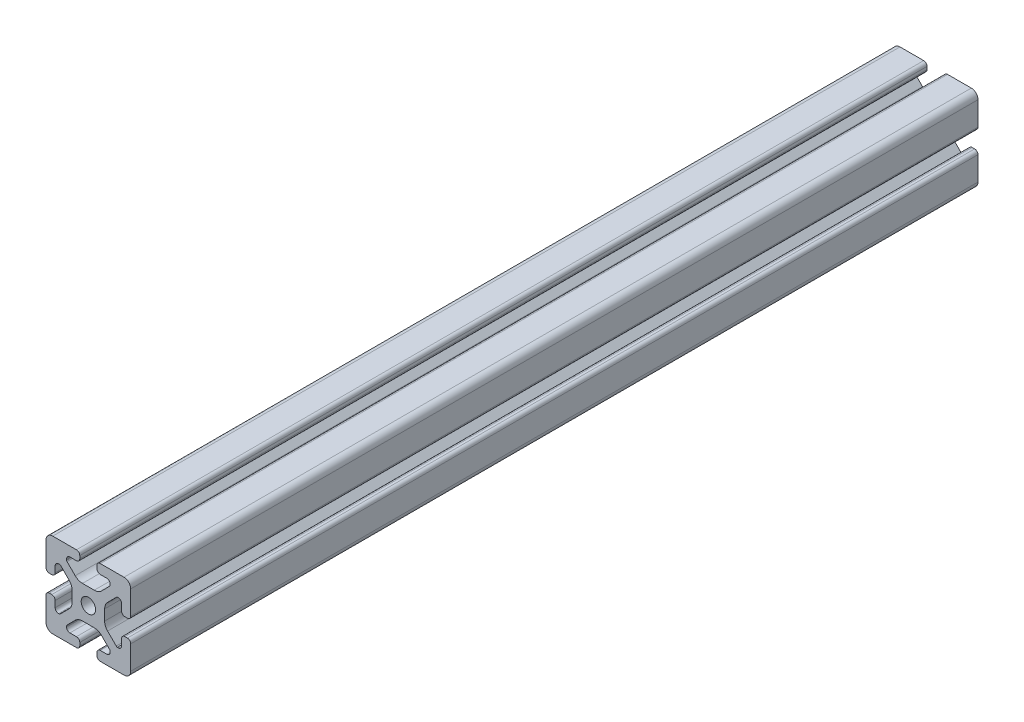
SolidWorks part; units mm, degrees
ref_plane "Front Plane" through (0, 0, 0) normal (0, 0, 1) x (1, 0, 0)
ref_plane "Top Plane" through (0, 0, 0) normal (0, 1, 0) x (1, 0, 0)
ref_plane "Right Plane" through (0, 0, 0) normal (1, 0, 0) x (0, 0, -1)
sketch "Sketch1" plane through (0, 0, 0) normal (0, 0, 1) x (1, 0, 0)
  line L0 (0, 19.7407) -> (0, -19.7407) construction
  line L1 (19.0335, 0) -> (-20.7246, 0) construction
  line L2 (-8.715, -15.5246) -> (-5.63, -15.5246)
  line L3 (-10.285, -13.9546) -> (-10.285, -13.4925)
  line L4 (-6.2171, -9.1098) -> (-10.0624, -12.9551)
  line L5 (2.7773, -7.685) -> (-2.7773, -7.685)
  line L6 (10.0624, -12.9551) -> (6.2171, -9.1098)
  line L7 (10.285, -13.9546) -> (10.285, -13.4925)
  line L8 (5.63, -15.5246) -> (8.715, -15.5246)
  line L9 (4.06, -18.43) -> (4.06, -17.0946)
  line L10 (-4.06, -18.43) -> (-4.06, -17.0946)
  line L11 (15.68, -8.7154) -> (15.68, -5.63)
  line L12 (-14.11, -10.2854) -> (-13.8169, -10.2854)
  line L13 (20, -16.83) -> (20, -5.63)
  line L14 (20, 5.63) -> (20, 13.0011)
  line L15 (-16.83, 20) -> (-5.63, 20)
  line L16 (5.63, 20) -> (12.9796, 20)
  line L17 (-8.715, 15.5246) -> (-5.63, 15.5246)
  line L18 (-20, -17.0184) -> (-20, -5.7579)
  line L19 (-20, 5.573) -> (-20, 13.0045)
  line L20 (-15.68, -8.7154) -> (-15.68, -5.7579)
  line L21 (-16.6746, -20) -> (-5.63, -20)
  line L22 (5.63, -20) -> (13, -20)
  line L23 (14.11, -10.2854) -> (13.6201, -10.2854)
  line L24 (13.1637, -9.947) -> (9.0762, -5.8595)
  line L25 (7.685, -2.5008) -> (7.685, 2.5008)
  line L26 (9.0762, 5.8595) -> (13.2795, 10.0628)
  line L27 (13.8169, 10.2854) -> (14.11, 10.2854)
  line L28 (15.68, 8.7154) -> (15.68, 5.63)
  line L29 (17.25, 4.06) -> (18.43, 4.06)
  line L30 (20, 13.0011) -> (20, 16.83)
  line L31 (16.83, 20) -> (12.9796, 20)
  line L32 (4.06, 18.43) -> (4.06, 17.0946)
  line L33 (5.63, 15.5246) -> (8.715, 15.5246)
  line L34 (10.285, 13.9546) -> (10.285, 13.4925)
  line L35 (10.0624, 12.9551) -> (6.2171, 9.1098)
  line L36 (2.7773, 7.685) -> (-2.7773, 7.685)
  line L37 (-6.2171, 9.1098) -> (-10.0624, 12.9551)
  line L38 (-10.285, 13.4925) -> (-10.285, 13.9546)
  line L39 (-4.06, 17.0946) -> (-4.06, 18.43)
  line L40 (-20, 16.83) -> (-20, 13.0045)
  line L41 (-18.43, 4.003) -> (-17.25, 4.003)
  line L42 (-15.68, 5.573) -> (-15.68, 8.4757)
  line L43 (-14.0552, 10.0447) -> (-13.7199, 10.033)
  line L44 (-13.0405, 9.8238) -> (-9.0762, 5.8595)
  line L45 (-7.685, 2.5008) -> (-7.685, -2.5008)
  line L46 (-9.0762, -5.8595) -> (-13.2795, -10.0628)
  line L47 (-17.2485, -4.1204) -> (-18.43, -4.1204)
  line L48 (13, -20) -> (16.83, -20)
  line L49 (18.43, -4.06) -> (17.25, -4.06)
  arc A0 (-5.63, -15.5246) -> (-4.06, -17.0946) centre (-5.63, -17.0946) cw
  arc A1 (-8.715, -15.5246) -> (-10.285, -13.9546) centre (-8.715, -13.9546) cw
  arc A2 (-10.285, -13.4925) -> (-10.0624, -12.9551) centre (-9.525, -13.4925) cw
  arc A3 (-6.2171, -9.1098) -> (-2.7773, -7.685) centre (-2.7773, -12.5496) cw
  arc A4 (2.7773, -7.685) -> (6.2171, -9.1098) centre (2.7773, -12.5496) cw
  arc A5 (10.0624, -12.9551) -> (10.285, -13.4925) centre (9.525, -13.4925) cw
  arc A6 (10.285, -13.9546) -> (8.715, -15.5246) centre (8.715, -13.9546) cw
  arc A7 (4.06, -17.0946) -> (5.63, -15.5246) centre (5.63, -17.0946) cw
  arc A8 (5.63, -20) -> (4.06, -18.43) centre (5.63, -18.43) cw
  arc A9 (-4.06, -18.43) -> (-5.63, -20) centre (-5.63, -18.43) cw
  circle A10 centre (0, 0) radius 3.4
  arc A11 (17.25, -4.06) -> (15.68, -5.63) centre (17.25, -5.63) ccw
  arc A12 (14.11, -10.2854) -> (15.68, -8.7154) centre (14.11, -8.7154) ccw
  arc A13 (13.1637, -9.947) -> (13.6201, -10.2854) centre (13.8117, -9.55) ccw
  arc A14 (7.685, -2.5008) -> (9.0762, -5.8595) centre (12.435, -2.5008) ccw
  arc A15 (9.0762, 5.8595) -> (7.685, 2.5008) centre (12.435, 2.5008) ccw
  arc A16 (13.8169, 10.2854) -> (13.2795, 10.0628) centre (13.8169, 9.5254) ccw
  arc A17 (15.68, 8.7154) -> (14.11, 10.2854) centre (14.11, 8.7154) ccw
  arc A18 (15.68, 5.63) -> (17.25, 4.06) centre (17.25, 5.63) ccw
  arc A19 (18.43, 4.06) -> (20, 5.63) centre (18.43, 5.63) ccw
  arc A20 (20, 16.83) -> (16.83, 20) centre (16.83, 16.83) ccw
  arc A21 (5.63, 20) -> (4.06, 18.43) centre (5.63, 18.43) ccw
  arc A22 (4.06, 17.0946) -> (5.63, 15.5246) centre (5.63, 17.0946) ccw
  arc A23 (10.285, 13.9546) -> (8.715, 15.5246) centre (8.715, 13.9546) ccw
  arc A24 (10.0624, 12.9551) -> (10.285, 13.4925) centre (9.525, 13.4925) ccw
  arc A25 (2.7773, 7.685) -> (6.2171, 9.1098) centre (2.7773, 12.5496) ccw
  arc A26 (-6.2171, 9.1098) -> (-2.7773, 7.685) centre (-2.7773, 12.5496) ccw
  arc A27 (-10.285, 13.4925) -> (-10.0624, 12.9551) centre (-9.525, 13.4925) ccw
  arc A28 (-8.715, 15.5246) -> (-10.285, 13.9546) centre (-8.715, 13.9546) ccw
  arc A29 (-5.63, 15.5246) -> (-4.06, 17.0946) centre (-5.63, 17.0946) ccw
  arc A30 (-4.06, 18.43) -> (-5.63, 20) centre (-5.63, 18.43) ccw
  arc A31 (-16.83, 20) -> (-20, 16.83) centre (-16.83, 16.83) ccw
  arc A32 (-20, 5.573) -> (-18.43, 4.003) centre (-18.43, 5.573) ccw
  arc A33 (-17.25, 4.003) -> (-15.68, 5.573) centre (-17.25, 5.573) ccw
  arc A34 (-14.0552, 10.0447) -> (-15.68, 8.4757) centre (-14.11, 8.4757) ccw
  arc A35 (-13.0405, 9.8238) -> (-13.7199, 10.033) centre (-13.5779, 9.2864) ccw
  arc A36 (-7.685, 2.5008) -> (-9.0762, 5.8595) centre (-12.435, 2.5008) ccw
  arc A37 (-9.0762, -5.8595) -> (-7.685, -2.5008) centre (-12.435, -2.5008) ccw
  arc A38 (-13.8169, -10.2854) -> (-13.2795, -10.0628) centre (-13.8169, -9.5254) ccw
  arc A39 (-15.68, -8.7154) -> (-14.11, -10.2854) centre (-14.11, -8.7154) ccw
  arc A40 (-15.68, -5.7579) -> (-17.2485, -4.1204) centre (-17.2485, -5.6904) ccw
  arc A41 (-18.43, -4.1204) -> (-20, -5.7579) centre (-18.4315, -5.6904) ccw
  arc A42 (-20, -17.0184) -> (-16.6746, -20) centre (-16.8354, -16.8341) ccw
  arc A43 (16.83, -20) -> (20, -16.83) centre (16.83, -16.83) ccw
  arc A44 (20, -5.63) -> (18.43, -4.06) centre (18.43, -5.63) ccw
  dimension "D1" = 6.8
  dimension "D2" = 4.32
  dimension "D3" = 15.37
  dimension "D4" = 20.57
  dimension "D5" = 15.37
  dimension "D6" = 40
  dimension "D7" = 20
  dimension "D8" = 4.32
  dimension "D9" = 8.12
extrude "Boss-Extrude1" add sketch "Sketch1" along normal blind 400
